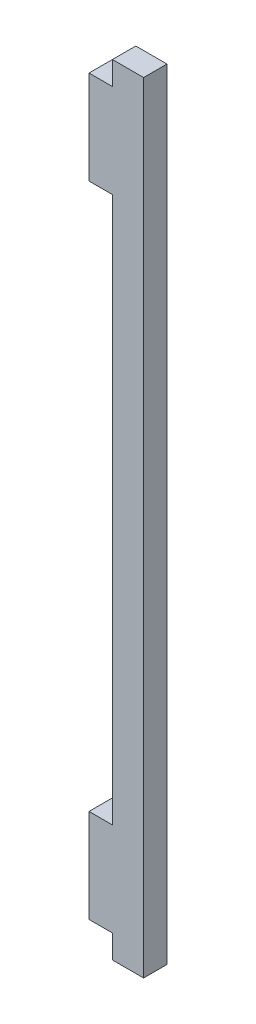
SolidWorks part; units mm, degrees
ref_plane "Alzado" through (0, 0, 0) normal (0, 0, 1) x (1, 0, 0)
ref_plane "Planta" through (0, 0, 0) normal (0, 1, 0) x (1, 0, 0)
ref_plane "Vista lateral" through (0, 0, 0) normal (1, 0, 0) x (0, 0, -1)
sketch "Croquis1" plane through (0, 0, 0) normal (0, 0, 1) x (1, 0, 0)
  line L0 (0, 50) -> (4, 50) construction
  line L1 (0, 0) -> (4, 0)
  line L2 (0, 0) -> (0, 3)
  line L3 (0, 100) -> (4, 100)
  line L4 (4, 0) -> (4, 100)
  line L5 (0, 97) -> (-3, 97)
  line L7 (0, 85) -> (-3, 85)
  line L8 (-3, 97) -> (-3, 85)
  line L9 (0, 15) -> (-3, 15)
  line L10 (-3, 3) -> (-3, 15)
  line L11 (0, 3) -> (-3, 3)
  line L13 (0, 97) -> (0, 100)
  line L14 (0, 15) -> (0, 85)
  dimension "D1" = 100
  dimension "D2" = 4
  dimension "D3" = 3
  dimension "D4" = 12
  dimension "D5" = 3
extrude "Saliente-Extruir1" add sketch "Croquis1" along normal blind 3
